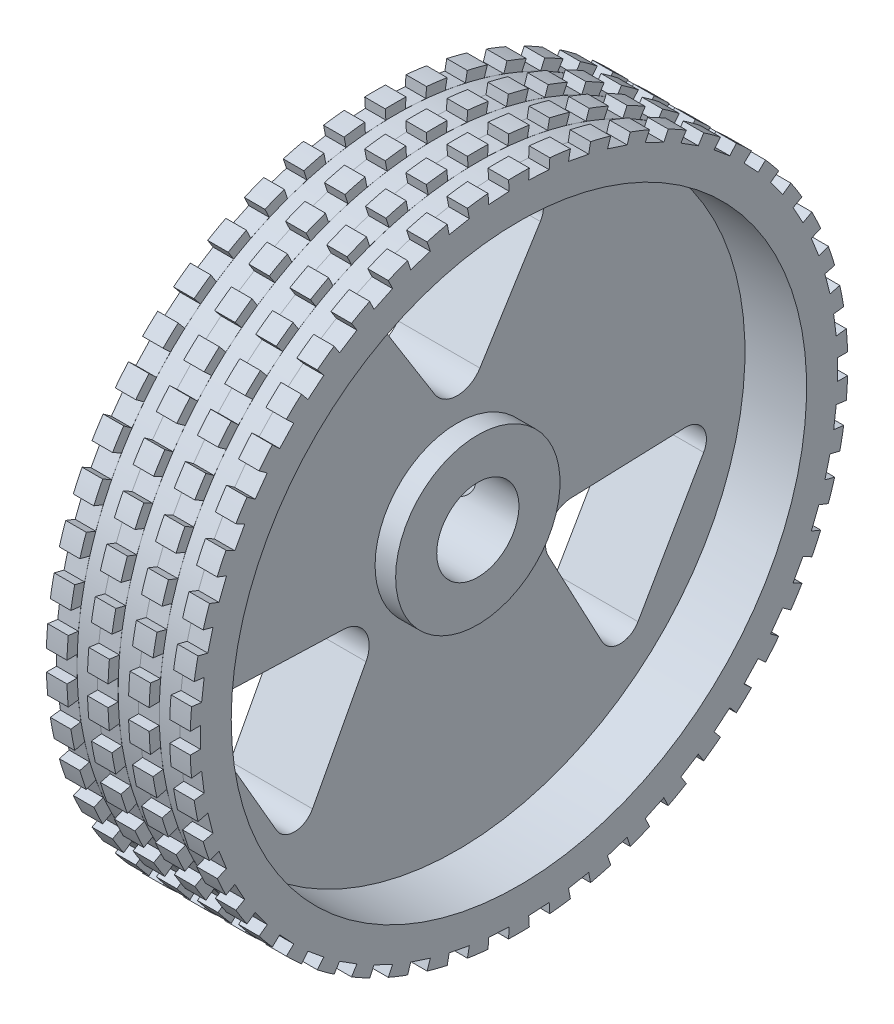
SolidWorks part; units mm, degrees
ref_plane "Front Plane" through (0, 0, 0) normal (0, 0, 1) x (1, 0, 0)
ref_plane "Top Plane" through (0, 0, 0) normal (0, 1, 0) x (1, 0, 0)
ref_plane "Right Plane" through (0, 0, 0) normal (1, 0, 0) x (0, 0, -1)
sketch "Sketch1" plane through (0, 0, 0) normal (0, 0, 1) x (1, 0, 0)
  line L0 (0, 2) -> (5, 2)
  line L1 (5, 4) -> (4, 4)
  line L2 (4, 4) -> (4, 14)
  line L3 (4, 14) -> (7, 14)
  line L4 (7, 14) -> (7, 16)
  line L5 (7, 16) -> (0, 16)
  line L6 (0, 16) -> (0, 2)
  line L7 (5, 2) -> (5, 4)
  line L8 (0, 0) -> (7.8014, 0) construction
  line L9 (0, 0) -> (0, 20.7668) construction
  dimension "D1" = 5
  dimension "D2" = 4
  dimension "D3" = 7
  dimension "D4" = 4
  dimension "D5" = 8
  dimension "D6" = 32
  dimension "D7" = 28
revolve "Revolve1" add sketch "Sketch1" angle 360 about L8
sketch "Sketch3" plane through (0, 0, 0) normal (0, 1, 0) x (1, 0, 0)
  line L0 (0, 0) -> (9.5614, 0) construction
  line L1 (0, 0) -> (0, 22.4251) construction
  line L2 (2, 0) -> (2, 16)
  line L3 (3.5, 16) -> (3.5, 11.5)
  line L4 (3.5, 11.5) -> (2.9, 11.5)
  line L5 (2.9, 11.5) -> (2.9, 0)
  line L6 (2.9, 0) -> (2, 0)
  line L7 (2, 16) -> (3.5, 16)
  line L8 (2, 0) -> (2, 29.6313) construction
  line L9 (0, 16) -> (7, 16) construction
  dimension "D1" = 1.8
  dimension "D2" = 4.5
  dimension "D3" = 2
  dimension "D4" = 3
revolve "Cut-Revolve2" cut sketch "Sketch3" angle 360 about L8
sketch "Sketch4" plane through (4, 0, 0) normal (1, 0, 0) x (0, 0, -1)
  line L0 (-5, 12) -> (5, 12)
  line L1 (5, 12) -> (0, 4)
  line L2 (0, 4) -> (-5, 12)
  line L3 (0, 0) -> (0, 20.2163) construction
  line L4 (12.8923, -1.6699) -> (7.8923, -10.3301)
  line L5 (3.4641, -2) -> (12.8923, -1.6699)
  line L6 (7.8923, -10.3301) -> (3.4641, -2)
  line L7 (-7.8923, -10.3301) -> (-12.8923, -1.6699)
  line L8 (-3.4641, -2) -> (-7.8923, -10.3301)
  line L9 (-12.8923, -1.6699) -> (-3.4641, -2)
  circle A1 centre (0, 0) radius 14 construction
  point P14 (0, 0)
  dimension "D4" = 12
  dimension "D1" = 8
  dimension "D3" = 10
  dimension "D2" = 3
extrude "Cut-Extrude1" cut sketch "Sketch4" against normal through all
fillet "Fillet2" radius 1 6 edges at (2, -10.3301, -7.8923) (2, -1.6699, -12.8923) (2, -10.3301, 7.8923) (2, -1.6699, 12.8923) (2, 12, -5) (2, 12, 5)
fillet "Fillet3" radius 1.3 3 edges at (2, 4, 0) (2, -2, 3.4641) (2, -2, -3.4641)
sketch "Sketch5" plane through (0, 0, 0) normal (0, 1, 0) x (1, 0, 0)
  line L0 (5, 16) -> (6, 16)
  line L1 (7, 16) -> (3.5, 16) construction
  line L2 (6, 16) -> (6, 15.5)
  line L3 (6, 15.5) -> (5, 15.5)
  line L4 (5, 15.5) -> (5, 16)
  line L5 (7, -16) -> (7, 16) construction
  line L6 (0, 0) -> (14.9903, 0) construction
  point P8 (5.5, 15.5)
  dimension "D1" = 1
  dimension "D2" = 0.5
  dimension "D3" = 1
revolve "Cut-Revolve3" cut sketch "Sketch5" angle 360 about L6
pattern_linear "LPattern1" count 3 spacing 2 along (-1, 0, 0) of "Cut-Revolve3"
sketch "Sketch9" plane through (0, 0, 0) normal (1, 0, 0) x (0, 0, -1)
  line L0 (0, 0) -> (25.8406, 0) construction
  line L5 (16, -0.5) -> (16, 0.5)
  line L6 (16, 0.5) -> (15.5, 0.5)
  line L7 (15.5, 0.5) -> (15.5, -0.5)
  line L8 (15.5, -0.5) -> (16, -0.5)
  circle A1 centre (0, 0) radius 16 construction
  dimension "D1" = 1
  dimension "D2" = 0.5
extrude "Cut-Extrude5" cut sketch "Sketch9" along normal through all
pattern_circular "CirPattern1" count 50 over 360 about axis through (0, 0, 0) along (1, 0, 0) of "Cut-Extrude5"
equation "\".5.00mm\"=2"
